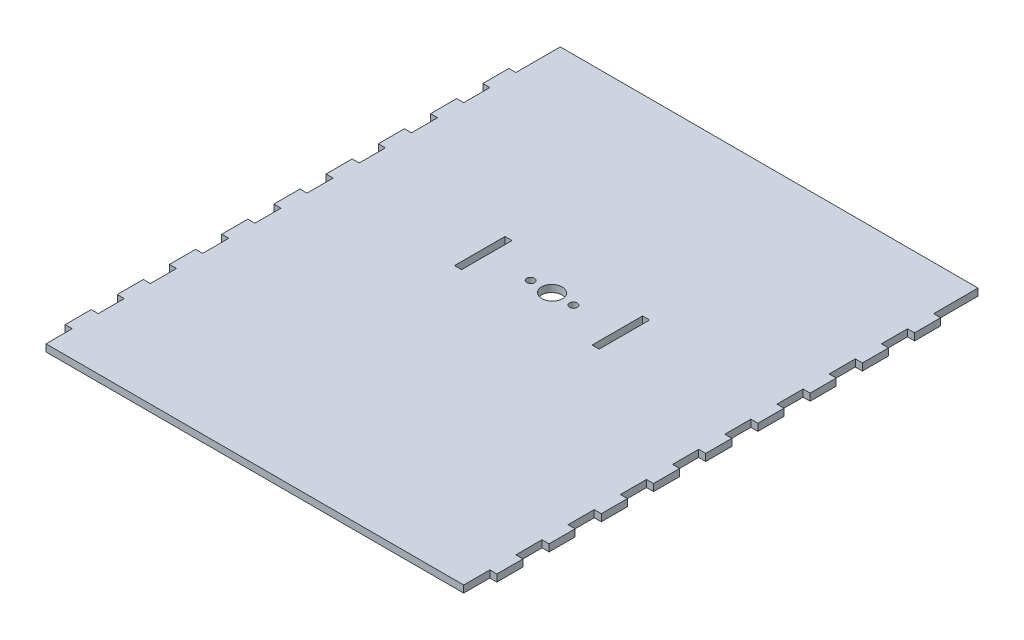
SolidWorks part; units mm, degrees
material "Maple"
ref_plane "Front Plane" through (0, 0, 0) normal (0, 0, 1) x (1, 0, 0)
ref_plane "Top Plane" through (0, 0, 0) normal (0, 1, 0) x (1, 0, 0)
ref_plane "Right Plane" through (0, 0, 0) normal (1, 0, 0) x (0, 0, -1)
sketch "Sketch1" plane through (0, 0, 0) normal (0, 1, 0) x (1, 0, 0)
  line L0 (0, -98.5) -> (0, 98.5) construction
  line L5 (-80, -98.5) -> (80, -98.5)
  line L6 (-80, -98.5) -> (-80, -88.5)
  line L32 (-80, 98.5) -> (80, 98.5)
  line L41 (80, -98.5) -> (80, -88.5)
  line L42 (-80, -98.5) -> (80, 98.5) construction
  line L43 (-80, 98.5) -> (80, -98.5) construction
  line L48 (-82.7, -68.5) -> (-82.7, -58.5)
  line L49 (-80, -58.5) -> (-82.7, -58.5)
  line L51 (80, -88.5) -> (82.7, -88.5)
  line L53 (80, -78.5) -> (82.7, -78.5)
  line L54 (82.7, -88.5) -> (82.7, -78.5)
  line L55 (80, -88.5) -> (82.7, -78.5) construction
  line L56 (80, -78.5) -> (82.7, -88.5) construction
  line L57 (-80, -88.5) -> (-82.7, -78.5) construction
  line L58 (-80, -78.5) -> (-82.7, -88.5) construction
  line L59 (-80, -88.5) -> (-82.7, -88.5)
  line L60 (-82.7, -88.5) -> (-82.7, -78.5)
  line L61 (-80, -78.5) -> (-82.7, -78.5)
  line L62 (82.7, -68.5) -> (82.7, -58.5)
  line L63 (80, -68.5) -> (82.7, -68.5)
  line L64 (80, -58.5) -> (82.7, -58.5)
  line L65 (82.7, -48.5) -> (82.7, -38.5)
  line L66 (80, -48.5) -> (82.7, -48.5)
  line L67 (80, -38.5) -> (82.7, -38.5)
  line L68 (82.7, -28.5) -> (82.7, -18.5)
  line L69 (80, -28.5) -> (82.7, -28.5)
  line L70 (80, -18.5) -> (82.7, -18.5)
  line L71 (82.7, -8.5) -> (82.7, 1.5)
  line L72 (80, -8.5) -> (82.7, -8.5)
  line L73 (80, 1.5) -> (82.7, 1.5)
  line L74 (82.7, 11.5) -> (82.7, 21.5)
  line L75 (80, 11.5) -> (82.7, 11.5)
  line L76 (80, 21.5) -> (82.7, 21.5)
  line L77 (82.7, 31.5) -> (82.7, 41.5)
  line L78 (80, 31.5) -> (82.7, 31.5)
  line L79 (80, 41.5) -> (82.7, 41.5)
  line L80 (82.7, 51.5) -> (82.7, 61.5)
  line L81 (80, 51.5) -> (82.7, 51.5)
  line L82 (80, 61.5) -> (82.7, 61.5)
  line L83 (82.7, 71.5) -> (82.7, 81.5)
  line L84 (80, 71.5) -> (82.7, 71.5)
  line L85 (80, 81.5) -> (82.7, 81.5)
  line L86 (82.7, -88.5) -> (82.7, -68.5) construction
  line L87 (-80, -68.5) -> (-82.7, -68.5)
  line L88 (-82.7, -48.5) -> (-82.7, -38.5)
  line L89 (-80, -38.5) -> (-82.7, -38.5)
  line L90 (-80, -48.5) -> (-82.7, -48.5)
  line L91 (-82.7, -28.5) -> (-82.7, -18.5)
  line L92 (-80, -18.5) -> (-82.7, -18.5)
  line L93 (-80, -28.5) -> (-82.7, -28.5)
  line L94 (-82.7, -8.5) -> (-82.7, 1.5)
  line L95 (-80, 1.5) -> (-82.7, 1.5)
  line L96 (-80, -8.5) -> (-82.7, -8.5)
  line L97 (-82.7, 11.5) -> (-82.7, 21.5)
  line L98 (-80, 21.5) -> (-82.7, 21.5)
  line L99 (-80, 11.5) -> (-82.7, 11.5)
  line L100 (-82.7, 31.5) -> (-82.7, 41.5)
  line L101 (-80, 41.5) -> (-82.7, 41.5)
  line L102 (-80, 31.5) -> (-82.7, 31.5)
  line L103 (-82.7, 51.5) -> (-82.7, 61.5)
  line L104 (-80, 61.5) -> (-82.7, 61.5)
  line L105 (-80, 51.5) -> (-82.7, 51.5)
  line L106 (-82.7, 71.5) -> (-82.7, 81.5)
  line L107 (-80, 81.5) -> (-82.7, 81.5)
  line L108 (-80, 71.5) -> (-82.7, 71.5)
  line L109 (-82.7, -88.5) -> (-82.7, -68.5) construction
  line L110 (-80, 81.5) -> (-80, 98.5)
  line L111 (-80, 61.5) -> (-80, 71.5)
  line L112 (-80, 41.5) -> (-80, 51.5)
  line L113 (-80, 21.5) -> (-80, 31.5)
  line L114 (-80, 1.5) -> (-80, 11.5)
  line L115 (-80, -18.5) -> (-80, -8.5)
  line L116 (-80, -38.5) -> (-80, -28.5)
  line L117 (-80, -58.5) -> (-80, -48.5)
  line L118 (-80, -78.5) -> (-80, -68.5)
  line L119 (80, -78.5) -> (80, -68.5)
  line L120 (80, -58.5) -> (80, -48.5)
  line L121 (80, -38.5) -> (80, -28.5)
  line L122 (80, 81.5) -> (80, 98.5)
  line L123 (80, 61.5) -> (80, 71.5)
  line L124 (80, 41.5) -> (80, 51.5)
  line L125 (80, 21.5) -> (80, 31.5)
  line L126 (80, 1.5) -> (80, 11.5)
  line L127 (80, -18.5) -> (80, -8.5)
  point P0 (0, 0)
  point P10 (84.7838, 75.2924)
  point P14 (0, 0)
  point P18 (81.35, -83.5)
  point P23 (-81.35, -83.5)
  dimension "D1" = 160
  dimension "D2" = 197
  dimension "D3" = 2.7
  dimension "D4" = 10
  dimension "D5" = 10
  dimension "D6" = 20
  dimension "D7" = 20
extrude "Boss-Extrude2" add sketch "Sketch1" along normal blind 2.7
sketch "Sketch2" plane through (0, 2.7, 0) normal (0, 1, 0) x (1, 0, 0)
  line L4 (25, 25.007) -> (25, 5.6884)
  line L5 (27.7, 25.007) -> (25, 25.007)
  line L6 (27.7, 5.6884) -> (27.7, 25.007)
  line L7 (25, 5.6884) -> (27.7, 5.6884)
  line L8 (25, 25.007) -> (25, 5.6884)
  line L9 (27.7, 25.007) -> (25, 25.007)
  line L10 (27.7, 5.6884) -> (27.7, 25.007)
  line L11 (25, 5.6884) -> (27.7, 5.6884)
  line L12 (-27.7, 5.6884) -> (-25, 5.6884)
  line L13 (-27.7, 25.007) -> (-27.7, 5.6884)
  line L14 (-25, 25.007) -> (-27.7, 25.007)
  line L15 (-25, 5.6884) -> (-25, 25.007)
  line L16 (-27.7, 5.6884) -> (-25, 5.6884)
  line L17 (-27.7, 25.007) -> (-27.7, 5.6884)
  line L18 (-25, 25.007) -> (-27.7, 25.007)
  line L19 (-25, 5.6884) -> (-25, 25.007)
  ellipse E1 centre (8.1925, 15.3477) end of major axis (9.6925, 15.3477) minor radius 1.4489
  ellipse E2 centre (8.1925, 15.3477) end of major axis (9.6925, 15.3477) minor radius 1.4489
  ellipse E3 centre (0, 15.3477) end of major axis (4, 15.3477) minor radius 3.8637
  ellipse E4 centre (0, 15.3477) end of major axis (4, 15.3477) minor radius 3.8637
  ellipse E5 centre (-8.1925, 15.3477) end of major axis (-9.6925, 15.3477) minor radius 1.4489
  ellipse E6 centre (-8.1925, 15.3477) end of major axis (-9.6925, 15.3477) minor radius 1.4489
  dimension "D1" = 0
  dimension "D2" = 0
  dimension "D3" = 0
  dimension "D4" = 0
  dimension "D5" = 0
extrude "Cut-Extrude1" cut sketch "Sketch2" against normal blind 3
